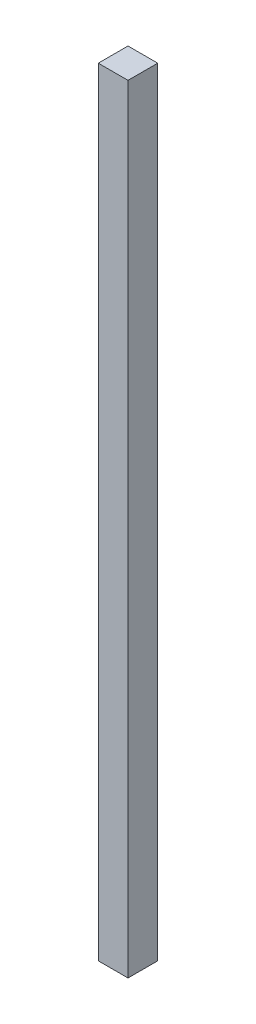
SolidWorks part; units mm, degrees
ref_plane "Front Plane" through (0, 0, 0) normal (0, 0, 1) x (1, 0, 0)
ref_plane "Top Plane" through (0, 0, 0) normal (0, 1, 0) x (1, 0, 0)
ref_plane "Right Plane" through (0, 0, 0) normal (1, 0, 0) x (0, 0, -1)
sketch "Sketch1" plane through (0, 0, 0) normal (0, 1, 0) x (1, 0, 0)
  line L1 (-44.45, -44.45) -> (44.45, -44.45)
  line L2 (-44.45, -44.45) -> (-44.45, 44.45)
  line L3 (-44.45, 44.45) -> (44.45, 44.45)
  line L4 (44.45, -44.45) -> (44.45, 44.45)
  line L5 (-44.45, -44.45) -> (44.45, 44.45) construction
  line L6 (-44.45, 44.45) -> (44.45, -44.45) construction
  point P0 (0, 0)
  dimension "D1" = 88.9
extrude "Boss-Extrude1" add sketch "Sketch1" along normal blind 2324.1 contours L3 L4 L1 L2
